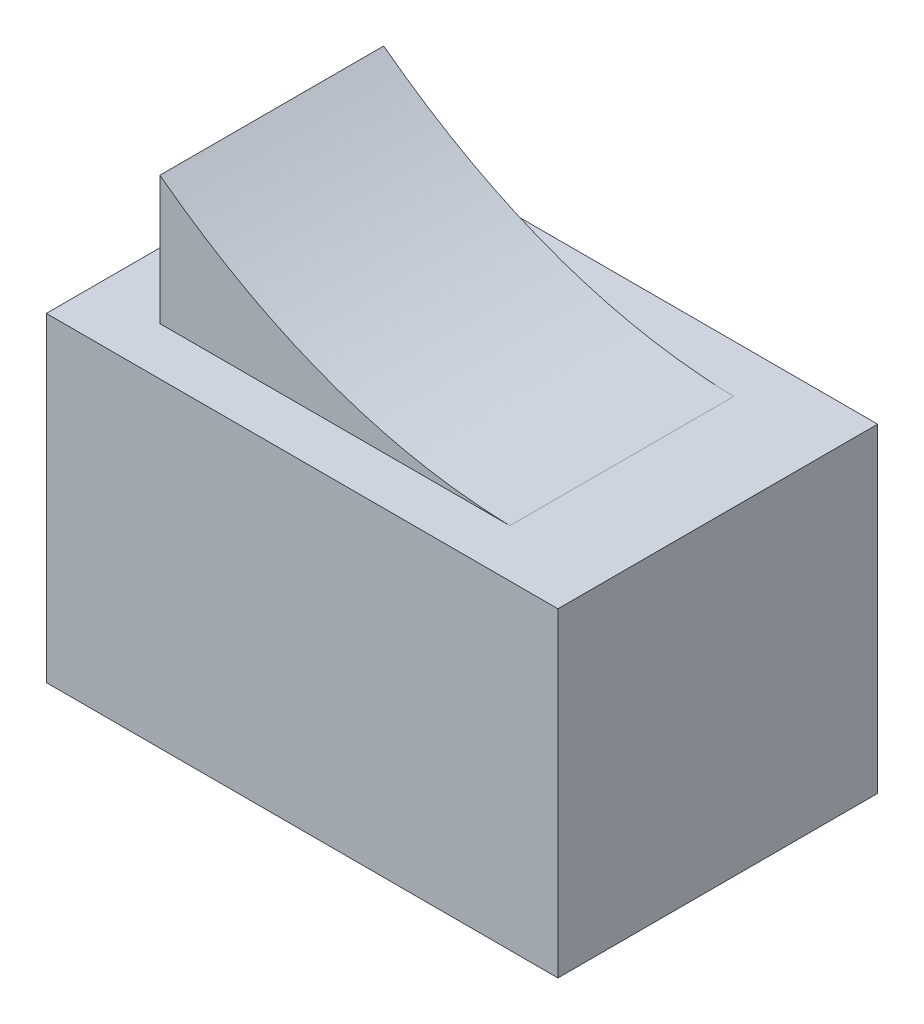
SolidWorks part; units mm, degrees
ref_plane "Front Plane" through (0, 0, 0) normal (0, 0, 1) x (1, 0, 0)
ref_plane "Top Plane" through (0, 0, 0) normal (0, 1, 0) x (1, 0, 0)
ref_plane "Right Plane" through (0, 0, 0) normal (1, 0, 0) x (0, 0, -1)
sketch "Sketch1" plane through (0, 0, 0) normal (0, 1, 0) x (1, 0, 0)
  line L1 (-10.16, -6.35) -> (10.16, -6.35)
  line L2 (-10.16, -6.35) -> (-10.16, 6.35)
  line L3 (-10.16, 6.35) -> (10.16, 6.35)
  line L4 (10.16, -6.35) -> (10.16, 6.35)
  line L5 (-10.16, -6.35) -> (10.16, 6.35) construction
  line L6 (-10.16, 6.35) -> (10.16, -6.35) construction
  point P0 (0, 0)
  dimension "D1" = 20.32
  dimension "D2" = 12.7
extrude "Boss-Extrude1" add sketch "Sketch1" along normal blind 12.7
ref_plane "Plane1" through (0, 0, 0) normal (0, 0, 1) x (1, 0, 0)
sketch "Sketch2" plane through (0, 0, 0) normal (0, 0, 1) x (1, 0, 0)
  line L0 (-7.5556, 12.7) -> (-7.5556, 17.8032)
  line L1 (-10.16, 12.7) -> (10.16, 12.7) construction
  line L2 (-7.5556, 12.7) -> (7.526, 12.7)
  spline S0 degree 2 poles (-7.5556, 17.8032) (-0.5044, 12.497) (7.526, 12.7) knots 0 0 0 1 1 1
extrude "Boss-Extrude2" add sketch "Sketch2" along normal mid plane 8.89 contours S0 L0 L2
